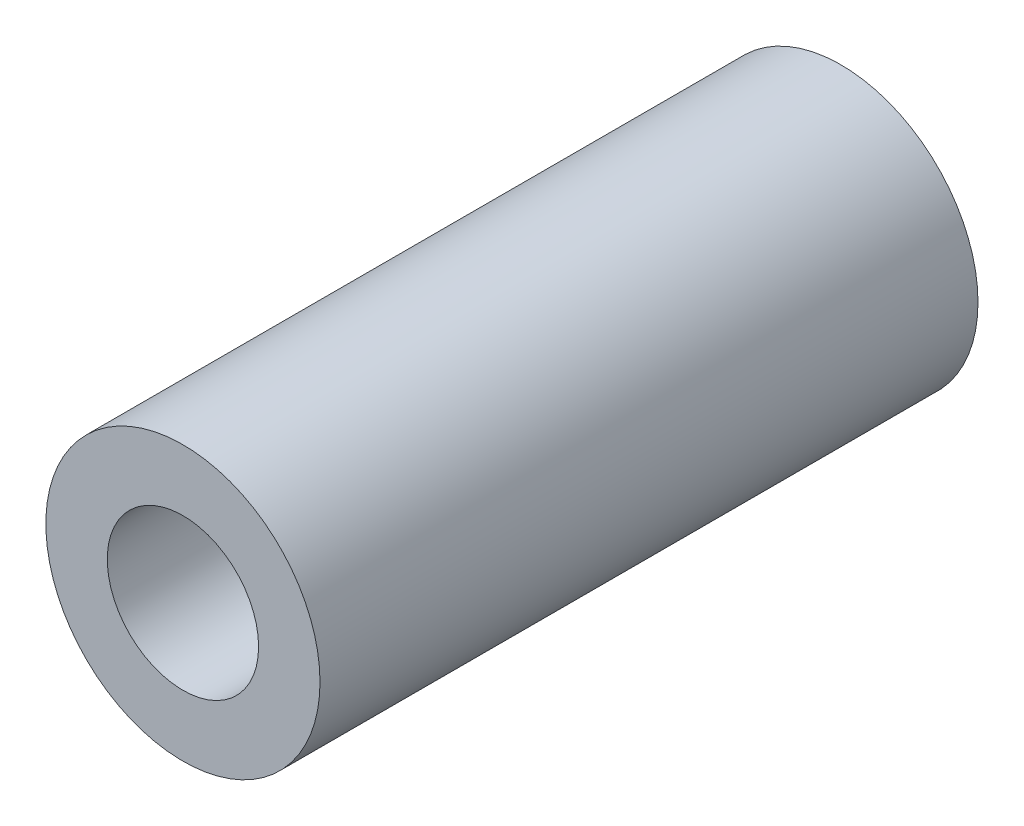
SolidWorks part; units mm, degrees
material "ABS"
ref_plane "Front Plane" through (0, 0, 0) normal (0, 0, 1) x (1, 0, 0)
ref_plane "Top Plane" through (0, 0, 0) normal (0, 1, 0) x (1, 0, 0)
ref_plane "Right Plane" through (0, 0, 0) normal (1, 0, 0) x (0, 0, -1)
sketch "Sketch1" plane through (0, 0, 0) normal (0, 0, 1) x (1, 0, 0)
  circle A0 centre (0, 0) radius 2.6289
  circle A1 centre (0, 0) radius 4.7625
  dimension "D1" = 5.2578
  dimension "D2" = 9.525
extrude "Boss-Extrude1" add sketch "Sketch1" along normal blind 22.86
